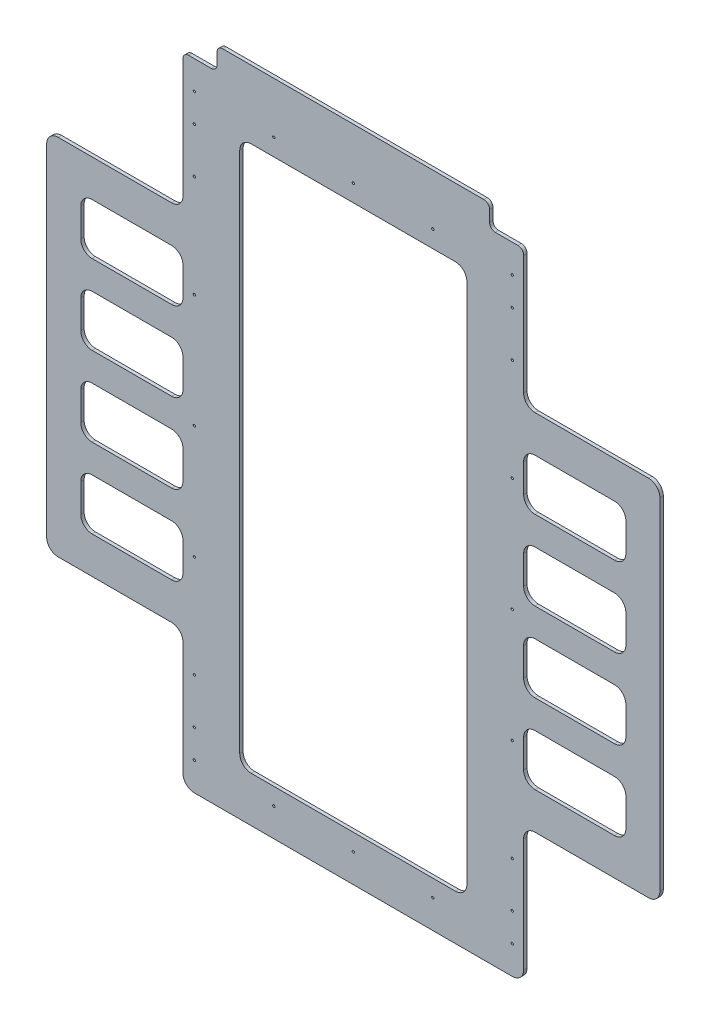
SolidWorks part; units mm, degrees
material "A-玻璃纤维"
ref_plane "前视基准面" through (0, 0, 0) normal (0, 0, 1) x (1, 0, 0)
ref_plane "上视基准面" through (0, 0, 0) normal (0, 1, 0) x (1, 0, 0)
ref_plane "右视基准面" through (0, 0, 0) normal (1, 0, 0) x (0, 0, -1)
other "Configuration Table"
sketch "草图1" plane through (0, 0, 0) normal (0, 0, 1) x (1, 0, 0)
  line L0 (-273.3288, 0) -> (-10, 0) construction
  line L1 (0, 10) -> (0, 290.5695) construction
  line L2 (-270, -150) -> (-270, 150)
  line L3 (-260, 160) -> (-160, 160)
  line L4 (-150, 170) -> (-150, 275)
  line L5 (-145, 280) -> (-125, 280)
  line L6 (150, 170) -> (150, 275)
  line L7 (260, 160) -> (160, 160)
  line L8 (270, -150) -> (270, 150)
  line L9 (260, -160) -> (160, -160)
  line L10 (150, -170) -> (150, -270)
  line L11 (-140, -280) -> (140, -280)
  line L12 (-150, -170) -> (-150, -270)
  line L13 (-260, -160) -> (-160, -160)
  line L14 (-120, 285) -> (-120, 295)
  line L15 (-90, 240) -> (90, 240)
  line L16 (-100, 230) -> (-100, -230)
  line L17 (-90, -240) -> (90, -240)
  line L18 (100, 230) -> (100, -230)
  line L19 (-100, 240) -> (100, -240) construction
  line L20 (-100, -240) -> (100, 240) construction
  line L21 (-115, 300) -> (115, 300)
  line L22 (120, 285) -> (120, 295)
  line L23 (125, 280) -> (145, 280)
  line L24 (-240, 47.5) -> (-240, 22.5)
  line L25 (-230, 127.5) -> (-160, 127.5)
  line L26 (-240, 117.5) -> (-240, 92.5)
  line L27 (-230, 82.5) -> (-160, 82.5)
  line L28 (-150, 117.5) -> (-150, 92.5)
  line L29 (-230, 57.5) -> (-160, 57.5)
  line L30 (-150, 47.5) -> (-150, 22.5)
  line L31 (-230, 12.5) -> (-160, 12.5)
  line L32 (-240, -22.5) -> (-240, -47.5)
  line L33 (-230, -12.5) -> (-160, -12.5)
  line L34 (-150, -22.5) -> (-150, -47.5)
  line L35 (-230, -57.5) -> (-160, -57.5)
  line L36 (-240, -92.5) -> (-240, -117.5)
  line L37 (-230, -82.5) -> (-160, -82.5)
  line L38 (-150, -92.5) -> (-150, -117.5)
  line L39 (-230, -127.5) -> (-160, -127.5)
  line L40 (-120, 285) -> (-120, 295)
  line L41 (120, 285) -> (120, 295)
  line L42 (145, 280) -> (125, 280)
  line L43 (150, 170) -> (150, 275)
  line L44 (260, 160) -> (160, 160)
  line L45 (270, -150) -> (270, 150)
  line L46 (260, -160) -> (160, -160)
  line L47 (150, -170) -> (150, -270)
  line L48 (-150, -170) -> (-150, -270)
  line L49 (-260, -160) -> (-160, -160)
  line L50 (-270, -150) -> (-270, 150)
  line L51 (-260, 160) -> (-160, 160)
  line L52 (-150, 170) -> (-150, 275)
  line L53 (-125, 280) -> (-145, 280)
  line L54 (230, -127.5) -> (160, -127.5)
  line L55 (150, -92.5) -> (150, -117.5)
  line L56 (230, -82.5) -> (160, -82.5)
  line L57 (240, -92.5) -> (240, -117.5)
  line L58 (230, -57.5) -> (160, -57.5)
  line L59 (150, -22.5) -> (150, -47.5)
  line L60 (230, -12.5) -> (160, -12.5)
  line L61 (240, -22.5) -> (240, -47.5)
  line L62 (230, 12.5) -> (160, 12.5)
  line L63 (150, 47.5) -> (150, 22.5)
  line L64 (230, 57.5) -> (160, 57.5)
  line L65 (150, 117.5) -> (150, 92.5)
  line L66 (230, 82.5) -> (160, 82.5)
  line L67 (240, 117.5) -> (240, 92.5)
  line L68 (230, 127.5) -> (160, 127.5)
  line L69 (240, 47.5) -> (240, 22.5)
  arc A0 (90, 240) -> (100, 230) centre (90, 230) cw
  arc A1 (-100, -230) -> (-90, -240) centre (-90, -230) ccw
  arc A2 (-90, 240) -> (-100, 230) centre (-90, 230) ccw
  arc A3 (90, -240) -> (100, -230) centre (90, -230) ccw
  arc A4 (-260, -160) -> (-270, -150) centre (-260, -150) cw
  arc A5 (-150, -170) -> (-160, -160) centre (-160, -170) ccw
  arc A6 (-140, -280) -> (-150, -270) centre (-140, -270) cw
  arc A7 (150, -270) -> (140, -280) centre (140, -270) cw
  arc A8 (260, -160) -> (270, -150) centre (260, -150) ccw
  arc A9 (160, -160) -> (150, -170) centre (160, -170) ccw
  arc A10 (260, 160) -> (270, 150) centre (260, 150) cw
  arc A11 (150, 170) -> (160, 160) centre (160, 170) ccw
  arc A12 (-160, 160) -> (-150, 170) centre (-160, 170) ccw
  arc A13 (-270, 150) -> (-260, 160) centre (-260, 150) cw
  arc A14 (-10, 0) -> (0, 10) centre (-10, 10) ccw construction
  arc A15 (120, 285) -> (125, 280) centre (125, 285) ccw
  arc A16 (120, 295) -> (115, 300) centre (115, 295) ccw
  arc A17 (-120, 295) -> (-115, 300) centre (-115, 295) cw
  arc A18 (-120, 285) -> (-125, 280) centre (-125, 285) cw
  arc A19 (-150, 275) -> (-145, 280) centre (-145, 275) cw
  arc A20 (150, 275) -> (145, 280) centre (145, 275) ccw
  arc A21 (-230, 127.5) -> (-240, 117.5) centre (-230, 117.5) ccw
  arc A22 (-150, 117.5) -> (-160, 127.5) centre (-160, 117.5) ccw
  arc A23 (-240, 92.5) -> (-230, 82.5) centre (-230, 92.5) ccw
  arc A24 (-160, 82.5) -> (-150, 92.5) centre (-160, 92.5) ccw
  arc A25 (-240, 22.5) -> (-230, 12.5) centre (-230, 22.5) ccw
  arc A26 (-230, 57.5) -> (-240, 47.5) centre (-230, 47.5) ccw
  arc A27 (-150, 47.5) -> (-160, 57.5) centre (-160, 47.5) ccw
  arc A28 (-160, 12.5) -> (-150, 22.5) centre (-160, 22.5) ccw
  arc A29 (-240, -47.5) -> (-230, -57.5) centre (-230, -47.5) ccw
  arc A30 (-230, -12.5) -> (-240, -22.5) centre (-230, -22.5) ccw
  arc A31 (-150, -22.5) -> (-160, -12.5) centre (-160, -22.5) ccw
  arc A32 (-160, -57.5) -> (-150, -47.5) centre (-160, -47.5) ccw
  arc A33 (-240, -117.5) -> (-230, -127.5) centre (-230, -117.5) ccw
  arc A34 (-230, -82.5) -> (-240, -92.5) centre (-230, -92.5) ccw
  arc A35 (-150, -92.5) -> (-160, -82.5) centre (-160, -92.5) ccw
  arc A36 (-160, -127.5) -> (-150, -117.5) centre (-160, -117.5) ccw
  arc A37 (-120, 295) -> (-115, 300) centre (-115, 295) cw
  arc A38 (120, 295) -> (115, 300) centre (115, 295) ccw
  arc A39 (120, 285) -> (125, 280) centre (125, 285) ccw
  arc A40 (150, 275) -> (145, 280) centre (145, 275) ccw
  arc A41 (160, 160) -> (150, 170) centre (160, 170) cw
  arc A42 (270, 150) -> (260, 160) centre (260, 150) ccw
  arc A43 (260, -160) -> (270, -150) centre (260, -150) ccw
  arc A44 (150, -170) -> (160, -160) centre (160, -170) cw
  arc A45 (140, -280) -> (150, -270) centre (140, -270) ccw
  arc A46 (-150, -270) -> (-140, -280) centre (-140, -270) ccw
  arc A47 (-160, -160) -> (-150, -170) centre (-160, -170) cw
  arc A48 (-260, -160) -> (-270, -150) centre (-260, -150) cw
  arc A49 (-260, 160) -> (-270, 150) centre (-260, 150) ccw
  arc A50 (-150, 170) -> (-160, 160) centre (-160, 170) cw
  arc A51 (-120, 285) -> (-125, 280) centre (-125, 285) cw
  arc A52 (-150, 275) -> (-145, 280) centre (-145, 275) cw
  arc A53 (160, -127.5) -> (150, -117.5) centre (160, -117.5) cw
  arc A54 (150, -92.5) -> (160, -82.5) centre (160, -92.5) cw
  arc A55 (230, -82.5) -> (240, -92.5) centre (230, -92.5) cw
  arc A56 (240, -117.5) -> (230, -127.5) centre (230, -117.5) cw
  arc A57 (160, -57.5) -> (150, -47.5) centre (160, -47.5) cw
  arc A58 (150, -22.5) -> (160, -12.5) centre (160, -22.5) cw
  arc A59 (230, -12.5) -> (240, -22.5) centre (230, -22.5) cw
  arc A60 (240, -47.5) -> (230, -57.5) centre (230, -47.5) cw
  arc A61 (160, 12.5) -> (150, 22.5) centre (160, 22.5) cw
  arc A62 (150, 47.5) -> (160, 57.5) centre (160, 47.5) cw
  arc A63 (230, 57.5) -> (240, 47.5) centre (230, 47.5) cw
  arc A64 (240, 22.5) -> (230, 12.5) centre (230, 22.5) cw
  arc A65 (160, 82.5) -> (150, 92.5) centre (160, 92.5) cw
  arc A66 (240, 92.5) -> (230, 82.5) centre (230, 92.5) cw
  arc A67 (150, 117.5) -> (160, 127.5) centre (160, 117.5) cw
  arc A68 (230, 127.5) -> (240, 117.5) centre (230, 117.5) cw
  point P3 (0, -213.5341)
  point P10 (0, 213.5341)
  point P14 (270, 0)
  point P19 (-270, 0)
  point P28 (0, 300)
  point P44 (-270, -160)
  point P47 (-150, -160)
  point P50 (-150, -280)
  point P53 (150, -280)
  point P56 (270, -160)
  point P59 (150, -160)
  point P62 (270, 160)
  point P65 (150, 160)
  point P68 (-150, 160)
  point P71 (-270, 160)
  point P74 (0, 0)
  point P77 (120, 280)
  point P80 (120, 300)
  point P83 (-120, 300)
  point P86 (-120, 280)
  point P89 (-150, 280)
  point P92 (150, 280)
  point P98 (-240, 127.5)
  point P101 (-150, 127.5)
  point P106 (-150, 82.5)
  dimension "D9" = 10
  dimension "D10" = 5
  dimension "D13" = 10
  dimension "D1" = 320
  dimension "D2" = 480
  dimension "D3" = 200
  dimension "D4" = 280
  dimension "D5" = 300
  dimension "D6" = 540
  dimension "D7" = 300
  dimension "D8" = 240
  dimension "D11" = 90
  dimension "D12" = 45
  dimension "D14" = 32.5
  dimension "D16" = 32.5
  dimension "D15" = 4
extrude "凸台-拉伸1" add sketch "草图1" along normal blind 3 contours L6 A20 L23 A15 L22 A16 L21 A17 L14 A18 L5 A19 L4 A12 L3 A13 L2 A4 L13 A5 L12 A6 L11 A7 L10 A9 L9 A8 L8 A10 L7 A11 A36 L39 A33 L36 A34 L37 A35 L38 A32 L35 A29 L32 A30 L33 A31 L34
sketch "草图2" plane through (0, 0, 3) normal (0, 0, 1) x (1, 0, 0)
  line L0 (-115, 300) -> (115, 300) construction
  line L1 (-94.6319, 0) -> (0, 0) construction
  line L2 (0, 0) -> (0, 105.5485) construction
  line L3 (-150, 170) -> (-150, 275) construction
  circle A0 centre (0, 255) radius 1
  circle A1 centre (70, 255) radius 1
  circle A2 centre (140, 255) radius 1
  circle A3 centre (-70, 255) radius 1
  circle A4 centre (-140, 255) radius 1
  circle A5 centre (-140, 0) radius 1
  circle A6 centre (-140, 100) radius 1
  circle A7 centre (-140, 190) radius 1
  circle A8 centre (-140, 230) radius 1
  circle A9 centre (-140, -230) radius 1
  circle A10 centre (-140, -190) radius 1
  circle A11 centre (-140, -100) radius 1
  circle A12 centre (-140, -255) radius 1
  circle A13 centre (-70, -255) radius 1
  circle A14 centre (140, -255) radius 1
  circle A15 centre (70, -255) radius 1
  circle A16 centre (0, -255) radius 1
  circle A17 centre (140, -100) radius 1
  circle A18 centre (140, -190) radius 1
  circle A19 centre (140, -230) radius 1
  circle A20 centre (140, 100) radius 1
  circle A21 centre (140, 0) radius 1
  circle A22 centre (140, 190) radius 1
  circle A23 centre (140, 230) radius 1
  dimension "D1" = 2
  dimension "D5" = 70
  dimension "D6" = 70
  dimension "D7" = 2
  dimension "D8" = 2
  dimension "D9" = 2
  dimension "D10" = 2
  dimension "D11" = 100
  dimension "D12" = 40
  dimension "D13" = 190
  dimension "D14" = 10
  dimension "D2" = 45
  dimension "D3" = 3
  dimension "D4" = 3
extrude "切除-拉伸1" cut sketch "草图2" against normal blind 3
sketch "草图3" plane through (0, 0, 3) normal (0, 0, 1) x (1, 0, 0)
  line L0 (-202.8961, 200) -> (-41.4358, 200) construction
  line L1 (-115, 300) -> (115, 300) construction
  circle A0 centre (-117.4552, 200) radius 1.25
  dimension "D1" = 2.5
  dimension "D2" = 100
